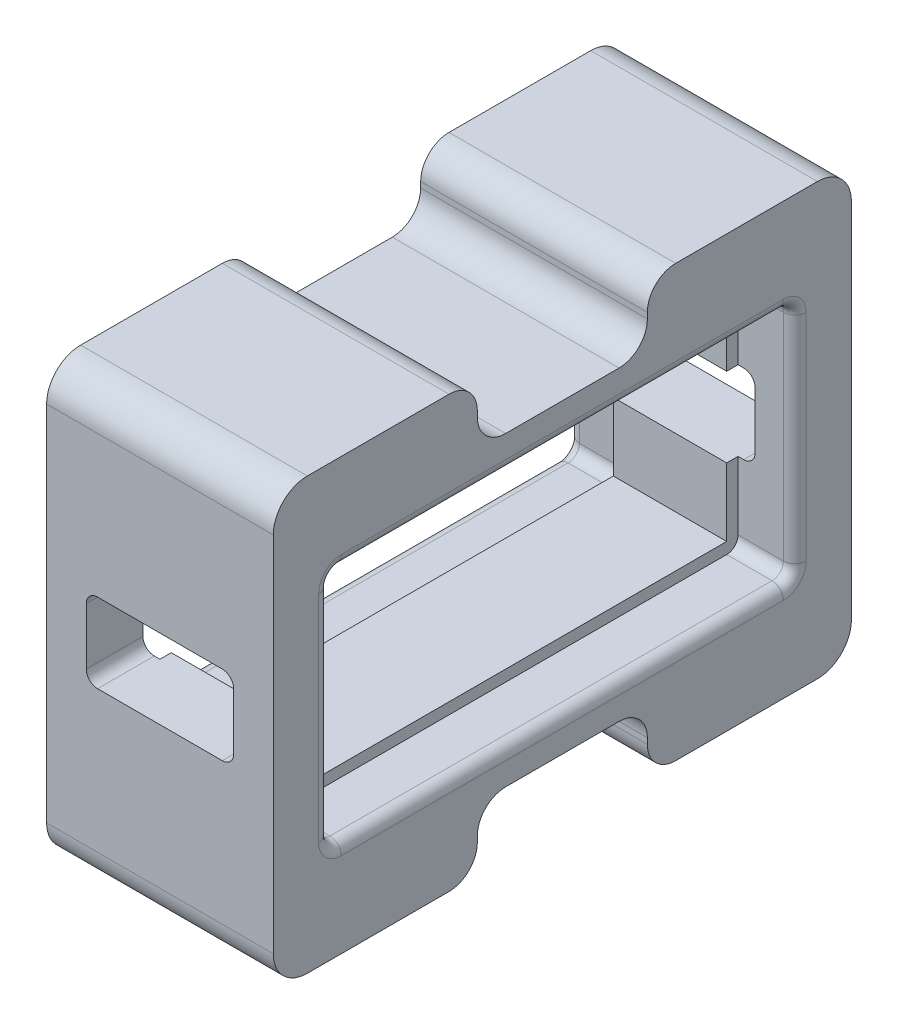
SolidWorks part; units mm, degrees
material "ABS"
ref_plane "Front Plane" through (0, 0, 0) normal (0, 0, 1) x (1, 0, 0)
ref_plane "Top Plane" through (0, 0, 0) normal (0, 1, 0) x (1, 0, 0)
ref_plane "Right Plane" through (0, 0, 0) normal (1, 0, 0) x (0, 0, -1)
sketch "Sketch1" plane through (0, 0, 0) normal (1, 0, 0) x (0, 0, -1)
  line L0 (-25.5, -19) -> (25.5, -19)
  line L1 (-25.5, -19) -> (-25.5, 19)
  line L2 (25.5, -19) -> (25.5, 19)
  line L3 (-25.5, 19) -> (25.5, 19)
  line L4 (-25.5, -19) -> (25.5, 19) construction
  line L5 (25.5, -19) -> (-25.5, 19) construction
  line L6 (-20.5, -10.5) -> (20.5, -10.5)
  line L7 (-20.5, -10.5) -> (-20.5, 10.5)
  line L8 (20.5, -10.5) -> (20.5, 10.5)
  line L9 (-20.5, 10.5) -> (20.5, 10.5)
  line L10 (-20.5, -10.5) -> (20.5, 10.5) construction
  line L11 (20.5, -10.5) -> (-20.5, 10.5) construction
  point P1 (0, 0)
  point P2 (0, 0)
  dimension "D1" = 38
  dimension "D2" = 51
  dimension "D3" = 41
  dimension "D4" = 21
extrude "Main Body" add sketch "Sketch1" along normal mid plane 20
sketch "Sketch2" plane through (0, 0, 0) normal (1, 0, 0) x (0, 0, -1)
  line L1 (-19.5, 9.5) -> (-19.5, -9.5)
  line L2 (-19.5, -9.5) -> (19.5, -9.5)
  line L3 (19.5, -9.5) -> (19.5, 9.5)
  line L4 (19.5, 9.5) -> (-19.5, 9.5)
  line L5 (-20.5, 10.5) -> (-20.5, -10.5)
  line L6 (20.5, 10.5) -> (-20.5, 10.5)
  line L7 (20.5, -10.5) -> (20.5, 10.5)
  line L8 (-20.5, -10.5) -> (20.5, -10.5)
  line L9 (-20.5, 10.5) -> (-20.5, -10.5)
  line L10 (20.5, 10.5) -> (-20.5, 10.5)
  line L11 (20.5, -10.5) -> (20.5, 10.5)
  line L12 (-20.5, -10.5) -> (20.5, -10.5)
  dimension "D1" = 0
  dimension "D2" = 1
extrude "Mid Servo Gap" add sketch "Sketch2" along normal mid plane 10
fillet "Edge Contouring" radius 1 11 edges at (7.5, 10.5, -20.5) (0, 9.5, -19.5) (-7.5, 10.5, -20.5) (-7.5, 10.5, 20.5) (0, 9.5, 19.5) (7.5, 10.5, 20.5) (0, -9.5, 19.5) (7.5, -10.5, 20.5) (7.5, -10.5, -20.5) (-7.5, -10.5, -20.5) (-7.5, -10.5, 20.5)
sketch "Sketch3" plane through (0, 0, 25.5) normal (0, 0, 1) x (1, 0, 0)
  line L0 (-10, 0) -> (10, 0) construction
  line L1 (-10, 19) -> (-10, -19) construction
  line L2 (10, 19) -> (10, -19) construction
  line L3 (0, 3.5) -> (0, 0) construction
  line L4 (-6.5, 3.5) -> (6.5, 3.5)
  line L5 (-6.5, 3.5) -> (-6.5, -3.5)
  line L6 (-6.5, -3.5) -> (6.5, -3.5)
  line L7 (6.5, 3.5) -> (6.5, -3.5)
  dimension "D1" = 7
  dimension "D2" = 13
extrude "Airway" cut sketch "Sketch3" against normal through all
sketch "Sketch4" plane through (10, 0, 0) normal (1, 0, 0) x (0, 0, -1)
  line L0 (0, 19) -> (0, -19) construction
  line L1 (25.5, 19) -> (-25.5, 19) construction
  line L2 (-25.5, -19) -> (25.5, -19) construction
  line L3 (19.5, 10.5) -> (-19.5, 10.5) construction
  line L4 (-7.5, 19) -> (7.5, 19)
  line L5 (-7.5, 19) -> (-7.5, 13.5)
  line L6 (-7.5, 13.5) -> (7.5, 13.5)
  line L7 (7.5, 19) -> (7.5, 13.5)
  line L8 (0, 0) -> (-25.5, 0) construction
  line L9 (-25.5, 19) -> (-25.5, -19) construction
  line L10 (-7.5, -19) -> (-7.5, -13.5)
  line L11 (-7.5, -13.5) -> (7.5, -13.5)
  line L12 (7.5, -19) -> (7.5, -13.5)
  line L13 (-7.5, -19) -> (7.5, -19)
  dimension "D1" = 3
  dimension "D2" = 15
extrude "Clearance - Cables" cut sketch "Sketch4" against normal through all
fillet "Contouring - Outer" radius 3 4 edges at (0, 19, -25.5) (0, -19, -25.5) (0, -19, 25.5) (0, 19, 25.5)
fillet "Contouring - Airway" radius 1 8 edges at (-6.5, 3.5, -23) (-6.5, -3.5, -23) (6.5, -3.5, -23) (6.5, 3.5, -23) (6.5, 3.5, 23) (6.5, -3.5, 23) (-6.5, -3.5, 23) (-6.5, 3.5, 23)
fillet "Contouring - Inner" radius 2.5 8 edges at (0, -19, -7.5) (0, -13.5, -7.5) (0, -19, 7.5) (0, -13.5, 7.5) (0, 19, -7.5) (0, 13.5, -7.5) (0, 13.5, 7.5) (0, 19, 7.5)
fillet "Clearance - Servo Insertion" radius 1 16 edges at (10, 10.2071, -20.2071) (10, 0, -20.5) (10, -10.2071, -20.2071) (10, -10.5, 0) (10, -10.2071, 20.2071) (10, 0, 20.5) (10, 10.2071, 20.2071) (-10, 10.2071, -20.2071) (-10, 0, -20.5) (-10, -10.2071, -20.2071) (-10, -10.5, 0) (-10, -10.2071, 20.2071) (-10, 0, 20.5) (-10, 10.2071, 20.2071) (10, 10.5, 0) (-10, 10.5, 0)
ref_point "Point1"
